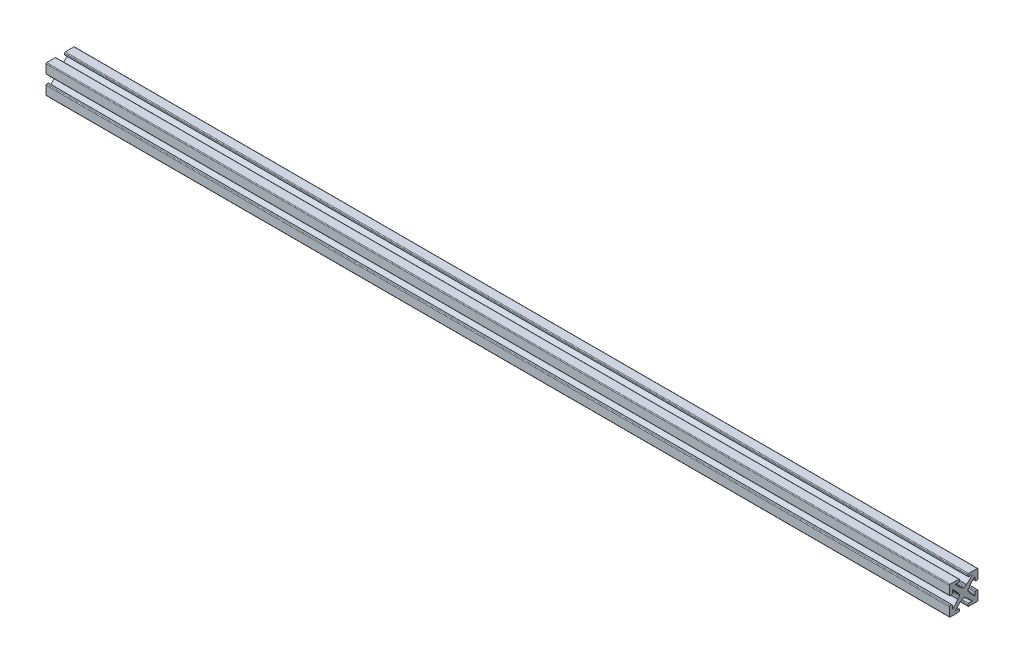
SolidWorks part; units mm, degrees
ref_plane "Front Plane" through (0, 0, 0) normal (0, 0, 1) x (1, 0, 0)
ref_plane "Top Plane" through (0, 0, 0) normal (0, 1, 0) x (1, 0, 0)
ref_plane "Right Plane" through (0, 0, 0) normal (1, 0, 0) x (0, 0, -1)
sketch "Sketch1" plane through (0, 0, 0) normal (1, 0, 0) x (0, 0, -1)
  line L0 (0, 0) -> (0, 1.4986) construction
  line L1 (-0.2413, 1.4986) -> (0.2413, 1.4986)
  line L2 (5.0038, 1.7526) -> (5.0038, 4.7498)
  line L3 (0.7493, 2.0066) -> (0.8899, 2.0066)
  line L4 (1.0639, 2.0756) -> (2.8908, 3.7937)
  line L5 (2.8038, 4.0132) -> (1.7526, 4.0132)
  line L6 (1.4986, 4.2672) -> (1.4986, 4.7498)
  line L7 (1.7526, 5.0038) -> (4.7498, 5.0038)
  line L8 (5.0038, 5.0038) -> (0, 0) construction
  line L9 (0, 0) -> (8.6271, 0) construction
  line L10 (0, 0) -> (0, 5.0038) construction
  line L11 (4.2672, 1.4986) -> (4.7498, 1.4986)
  line L12 (4.0132, 2.8038) -> (4.0132, 1.7526)
  line L13 (2.0756, 1.0639) -> (3.7937, 2.8908)
  line L14 (2.0066, 0.7493) -> (2.0066, 0.8899)
  line L15 (1.4986, -0.2413) -> (1.4986, 0.2413)
  line L16 (0, 0) -> (1.4986, 0) construction
  line L17 (-0.2413, -1.4986) -> (0.2413, -1.4986)
  line L18 (0.7493, -2.0066) -> (0.8899, -2.0066)
  line L19 (1.0639, -2.0756) -> (2.8908, -3.7937)
  line L20 (2.8038, -4.0132) -> (1.7526, -4.0132)
  line L21 (1.4986, -4.2672) -> (1.4986, -4.7498)
  line L22 (1.7526, -5.0038) -> (4.7498, -5.0038)
  line L23 (5.0038, -1.7526) -> (5.0038, -4.7498)
  line L24 (4.2672, -1.4986) -> (4.7498, -1.4986)
  line L25 (4.0132, -2.8038) -> (4.0132, -1.7526)
  line L26 (2.0756, -1.0639) -> (3.7937, -2.8908)
  line L27 (2.0066, -0.7493) -> (2.0066, -0.8899)
  line L28 (-0.7493, 2.0066) -> (-0.8899, 2.0066)
  line L29 (-1.0639, 2.0756) -> (-2.8908, 3.7937)
  line L30 (-2.8038, 4.0132) -> (-1.7526, 4.0132)
  line L31 (-1.4986, 4.2672) -> (-1.4986, 4.7498)
  line L32 (-1.7526, 5.0038) -> (-4.7498, 5.0038)
  line L33 (-5.0038, 1.7526) -> (-5.0038, 4.7498)
  line L34 (-4.2672, 1.4986) -> (-4.7498, 1.4986)
  line L35 (-4.0132, 2.8038) -> (-4.0132, 1.7526)
  line L36 (-2.0756, 1.0639) -> (-3.7937, 2.8908)
  line L37 (-2.0066, 0.7493) -> (-2.0066, 0.8899)
  line L38 (-1.4986, -0.2413) -> (-1.4986, 0.2413)
  line L39 (-2.0066, -0.7493) -> (-2.0066, -0.8899)
  line L40 (-2.0756, -1.0639) -> (-3.7937, -2.8908)
  line L41 (-4.0132, -2.8038) -> (-4.0132, -1.7526)
  line L42 (-4.2672, -1.4986) -> (-4.7498, -1.4986)
  line L43 (-5.0038, -1.7526) -> (-5.0038, -4.7498)
  line L44 (-1.7526, -5.0038) -> (-4.7498, -5.0038)
  line L45 (-1.4986, -4.2672) -> (-1.4986, -4.7498)
  line L46 (-2.8038, -4.0132) -> (-1.7526, -4.0132)
  line L47 (-1.0639, -2.0756) -> (-2.8908, -3.7937)
  line L48 (-0.7493, -2.0066) -> (-0.8899, -2.0066)
  arc A0 (2.8908, 3.7937) -> (2.8038, 4.0132) centre (2.8038, 3.8862) ccw
  arc A1 (0.4953, 1.7526) -> (0.7493, 2.0066) centre (0.7493, 1.7526) cw
  arc A2 (0.8899, 2.0066) -> (1.0639, 2.0756) centre (0.8899, 2.2606) ccw
  arc A3 (1.7526, 4.0132) -> (1.4986, 4.2672) centre (1.7526, 4.2672) cw
  arc A4 (1.4986, 4.7498) -> (1.7526, 5.0038) centre (1.7526, 4.7498) cw
  arc A5 (0.2413, 1.4986) -> (0.4953, 1.7526) centre (0.2413, 1.7526) ccw
  arc A6 (4.7498, 1.4986) -> (5.0038, 1.7526) centre (4.7498, 1.7526) ccw
  arc A7 (4.0132, 1.7526) -> (4.2672, 1.4986) centre (4.2672, 1.7526) ccw
  arc A8 (3.7937, 2.8908) -> (4.0132, 2.8038) centre (3.8862, 2.8038) cw
  arc A9 (2.0066, 0.8899) -> (2.0756, 1.0639) centre (2.2606, 0.8899) cw
  arc A10 (1.7526, 0.4953) -> (2.0066, 0.7493) centre (1.7526, 0.7493) ccw
  arc A11 (1.4986, 0.2413) -> (1.7526, 0.4953) centre (1.7526, 0.2413) cw
  arc A12 (0.2413, -1.4986) -> (0.4953, -1.7526) centre (0.2413, -1.7526) cw
  arc A13 (0.4953, -1.7526) -> (0.7493, -2.0066) centre (0.7493, -1.7526) ccw
  arc A14 (0.8899, -2.0066) -> (1.0639, -2.0756) centre (0.8899, -2.2606) cw
  arc A15 (2.8908, -3.7937) -> (2.8038, -4.0132) centre (2.8038, -3.8862) cw
  arc A16 (1.7526, -4.0132) -> (1.4986, -4.2672) centre (1.7526, -4.2672) ccw
  arc A17 (1.4986, -4.7498) -> (1.7526, -5.0038) centre (1.7526, -4.7498) ccw
  arc A18 (4.7498, -1.4986) -> (5.0038, -1.7526) centre (4.7498, -1.7526) cw
  arc A19 (4.0132, -1.7526) -> (4.2672, -1.4986) centre (4.2672, -1.7526) cw
  arc A20 (3.7937, -2.8908) -> (4.0132, -2.8038) centre (3.8862, -2.8038) ccw
  arc A21 (2.0066, -0.8899) -> (2.0756, -1.0639) centre (2.2606, -0.8899) ccw
  arc A22 (1.7526, -0.4953) -> (2.0066, -0.7493) centre (1.7526, -0.7493) cw
  arc A23 (1.4986, -0.2413) -> (1.7526, -0.4953) centre (1.7526, -0.2413) ccw
  arc A24 (-0.2413, 1.4986) -> (-0.4953, 1.7526) centre (-0.2413, 1.7526) cw
  arc A25 (-0.4953, 1.7526) -> (-0.7493, 2.0066) centre (-0.7493, 1.7526) ccw
  arc A26 (-0.8899, 2.0066) -> (-1.0639, 2.0756) centre (-0.8899, 2.2606) cw
  arc A27 (-2.8908, 3.7937) -> (-2.8038, 4.0132) centre (-2.8038, 3.8862) cw
  arc A28 (-1.7526, 4.0132) -> (-1.4986, 4.2672) centre (-1.7526, 4.2672) ccw
  arc A29 (-1.4986, 4.7498) -> (-1.7526, 5.0038) centre (-1.7526, 4.7498) ccw
  arc A30 (-4.7498, 1.4986) -> (-5.0038, 1.7526) centre (-4.7498, 1.7526) cw
  arc A31 (-4.0132, 1.7526) -> (-4.2672, 1.4986) centre (-4.2672, 1.7526) cw
  arc A32 (-3.7937, 2.8908) -> (-4.0132, 2.8038) centre (-3.8862, 2.8038) ccw
  arc A33 (-2.0066, 0.8899) -> (-2.0756, 1.0639) centre (-2.2606, 0.8899) ccw
  arc A34 (-1.7526, 0.4953) -> (-2.0066, 0.7493) centre (-1.7526, 0.7493) cw
  arc A35 (-1.4986, 0.2413) -> (-1.7526, 0.4953) centre (-1.7526, 0.2413) ccw
  arc A36 (-1.4986, -0.2413) -> (-1.7526, -0.4953) centre (-1.7526, -0.2413) cw
  arc A37 (-1.7526, -0.4953) -> (-2.0066, -0.7493) centre (-1.7526, -0.7493) ccw
  arc A38 (-2.0066, -0.8899) -> (-2.0756, -1.0639) centre (-2.2606, -0.8899) cw
  arc A39 (-3.7937, -2.8908) -> (-4.0132, -2.8038) centre (-3.8862, -2.8038) cw
  arc A40 (-4.0132, -1.7526) -> (-4.2672, -1.4986) centre (-4.2672, -1.7526) ccw
  arc A41 (-4.7498, -1.4986) -> (-5.0038, -1.7526) centre (-4.7498, -1.7526) ccw
  arc A42 (-1.4986, -4.7498) -> (-1.7526, -5.0038) centre (-1.7526, -4.7498) cw
  arc A43 (-1.7526, -4.0132) -> (-1.4986, -4.2672) centre (-1.7526, -4.2672) cw
  arc A44 (-2.8908, -3.7937) -> (-2.8038, -4.0132) centre (-2.8038, -3.8862) ccw
  arc A45 (-0.8899, -2.0066) -> (-1.0639, -2.0756) centre (-0.8899, -2.2606) ccw
  arc A46 (-0.4953, -1.7526) -> (-0.7493, -2.0066) centre (-0.7493, -1.7526) cw
  arc A47 (-0.2413, -1.4986) -> (-0.4953, -1.7526) centre (-0.2413, -1.7526) ccw
  arc A48 (-4.7498, 5.0038) -> (-5.0038, 4.7498) centre (-4.7498, 4.7498) ccw
  arc A49 (-5.0038, -4.7498) -> (-4.7498, -5.0038) centre (-4.7498, -4.7498) ccw
  arc A50 (4.7498, -5.0038) -> (5.0038, -4.7498) centre (4.7498, -4.7498) ccw
  arc A51 (4.7498, 5.0038) -> (5.0038, 4.7498) centre (4.7498, 4.7498) cw
  point P14 (3.1242, 4.0132)
  point P19 (0.9906, 2.0066)
  point P150 (0, -1.4986)
  point P152 (-5.0038, 5.0038)
  point P155 (-5.0038, -5.0038)
  point P158 (5.0038, -5.0038)
  dimension "D10" = 0.127
  dimension "D11" = 0.254
  dimension "D2" = 0.254
  dimension "D1" = 10.0076
  dimension "D3" = 2.9972
  dimension "D4" = 0.508
  dimension "D5" = 2.9972
  dimension "D6" = 0.9906
  dimension "D7" = 1.6256
  dimension "D8" = 1.9812
  dimension "D9" = 0.9906
extrude "Boss.-Extru.1" add sketch "Sketch1" along normal blind 316.5
